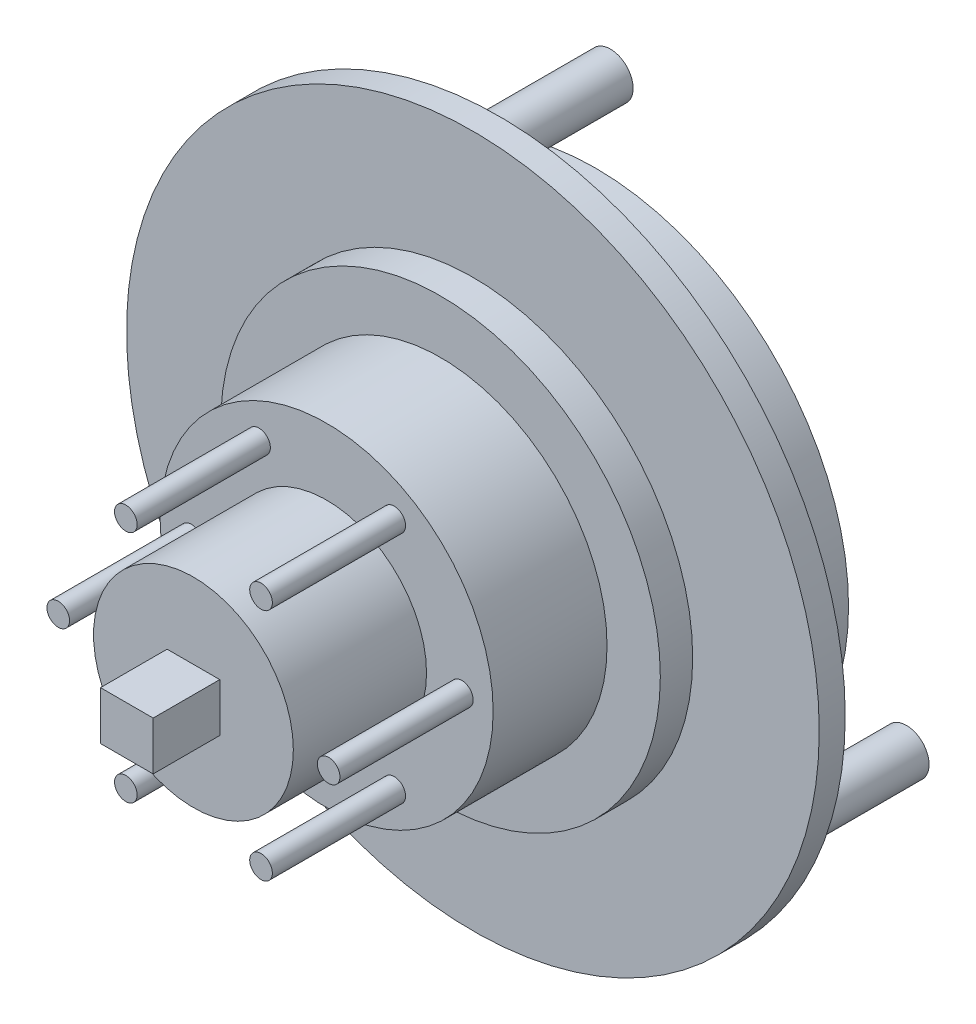
SolidWorks part; units mm, degrees
ref_plane "Front Plane" through (0, 0, 0) normal (0, 0, 1) x (1, 0, 0)
ref_plane "Top Plane" through (0, 0, 0) normal (0, 1, 0) x (1, 0, 0)
ref_plane "Right Plane" through (0, 0, 0) normal (1, 0, 0) x (0, 0, -1)
sketch "Sketch1" plane through (0, 0, 0) normal (0, 0, 1) x (1, 0, 0)
  circle A0 centre (0, 0) radius 26
  dimension "D1" = 52
extrude "Boss-Extrude1" add sketch "Sketch1" along normal blind 1.95
sketch "Sketch2" plane through (0, 0, 0) normal (0, 0, -1) x (-1, 0, 0)
  circle A0 centre (0, 0) radius 19
  dimension "D1" = 38
extrude "Boss-Extrude2" add sketch "Sketch2" along normal blind 7.25
sketch "Sketch3" plane through (0, 0, 1.95) normal (0, 0, 1) x (1, 0, 0)
  circle A0 centre (0, 0) radius 16.5
  dimension "D1" = 33
extrude "Boss-Extrude3" add sketch "Sketch3" along normal blind 2.43
sketch "Sketch4" plane through (0, 0, 4.38) normal (0, 0, 1) x (1, 0, 0)
  circle A0 centre (0, 0) radius 12.5
  dimension "D1" = 25
extrude "Boss-Extrude4" add sketch "Sketch4" along normal blind 8.55
sketch "Sketch5" plane through (0, 0, 12.93) normal (0, 0, 1) x (1, 0, 0)
  circle A0 centre (0, 0) radius 7.5
  dimension "D1" = 15
extrude "Boss-Extrude5" add sketch "Sketch5" along normal blind 10
sketch "Sketch6" plane through (0, 0, 0) normal (0, 0, -1) x (-1, 0, 0)
  line L0 (21.538, -14.5642) -> (0, 0) construction
  line L1 (0, 0) -> (18.97, -12.8277) construction
  line L2 (0, 0) -> (-20.5941, -10.0147) construction
  circle A0 centre (0, 0) radius 26 construction
  circle A1 centre (18.97, -12.8277) radius 1.7
  circle A2 centre (-20.5941, -10.0147) radius 1.7
  circle A3 centre (1.6241, 22.8423) radius 1.7
  dimension "D2" = 3.4
  dimension "D1" = 3.1
  dimension "D4" = 120
  dimension "D5" = 22.9
  dimension "D3" = 3
extrude "Boss-Extrude6" add sketch "Sketch6" along normal blind 10
sketch "Sketch7" plane through (0, 0, 12.93) normal (0, 0, 1) x (1, 0, 0)
  line L0 (-12.5, 0) -> (0, 0) construction
  line L1 (0, 0) -> (-10.15, 0) construction
  circle A0 centre (0, 0) radius 12.5 construction
  circle A1 centre (-10.15, 0) radius 0.85
  circle A2 centre (-5.075, 8.7902) radius 0.85
  circle A3 centre (5.075, 8.7902) radius 0.85
  circle A4 centre (10.15, 0) radius 0.85
  circle A5 centre (5.075, -8.7902) radius 0.85
  circle A6 centre (-5.075, -8.7902) radius 0.85
  dimension "D1" = 1.7
  dimension "D2" = 2.35
  dimension "D4" = 10.15
  dimension "D3" = 6
extrude "Boss-Extrude7" add sketch "Sketch7" along normal blind 10
sketch "Sketch8" plane through (0, 0, 22.93) normal (0, 0, 1) x (1, 0, 0)
  line L1 (1.9766, 1.8172) -> (-1.9766, 1.8172)
  line L2 (1.9766, 1.8172) -> (1.9766, -1.8172)
  line L3 (1.9766, -1.8172) -> (-1.9766, -1.8172)
  line L4 (-1.9766, 1.8172) -> (-1.9766, -1.8172)
  line L5 (1.9766, 1.8172) -> (-1.9766, -1.8172) construction
  line L6 (1.9766, -1.8172) -> (-1.9766, 1.8172) construction
  point P0 (0, 0)
extrude "Boss-Extrude8" add sketch "Sketch8" along normal blind 5
